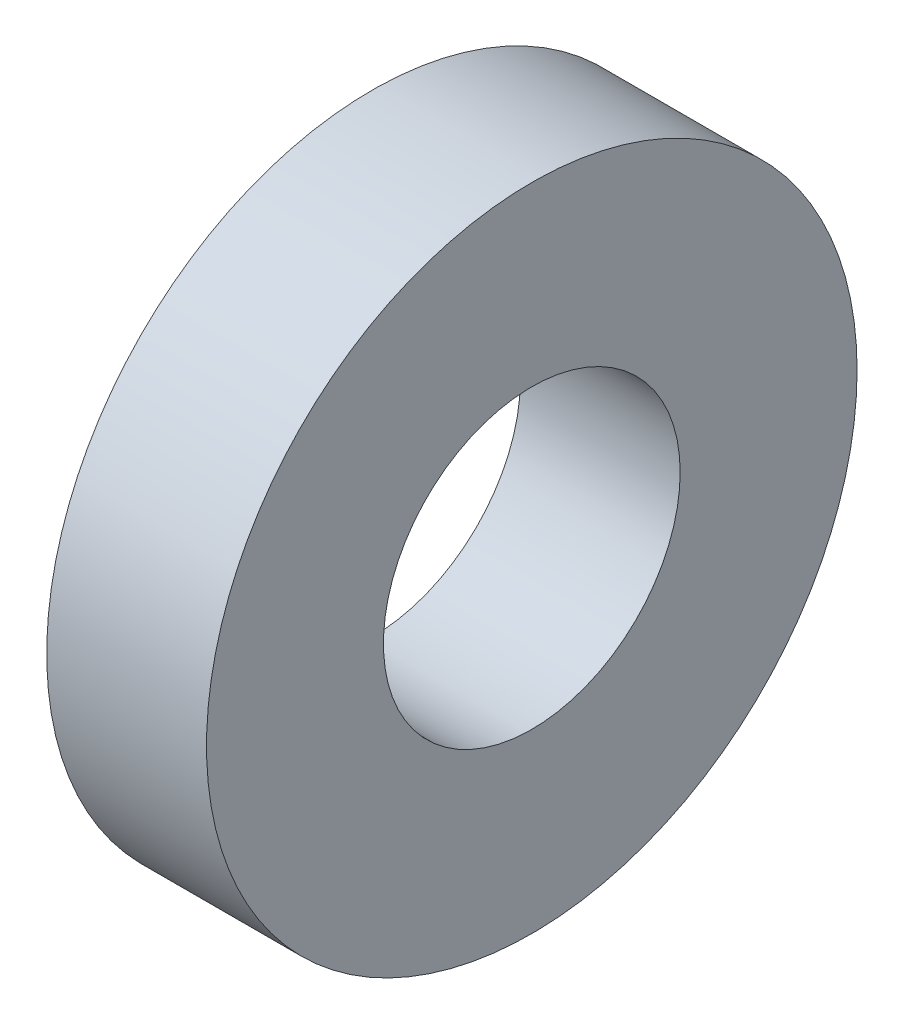
SolidWorks part; units mm, degrees
ref_plane "Front Plane" through (0, 0, 0) normal (0, 0, 1) x (1, 0, 0)
ref_plane "Top Plane" through (0, 0, 0) normal (0, 1, 0) x (1, 0, 0)
ref_plane "Right Plane" through (0, 0, 0) normal (1, 0, 0) x (0, 0, -1)
sketch "Sketch1" plane through (0, 0, 0) normal (1, 0, 0) x (0, 0, -1)
  circle A0 centre (0, 0) radius 3.6195
  circle A1 centre (0, 0) radius 1.651
  dimension "OD" = 7.239
  dimension "ID" = 3.302
extrude "Boss-Extrude1" add sketch "Sketch1" along normal blind 1.778
